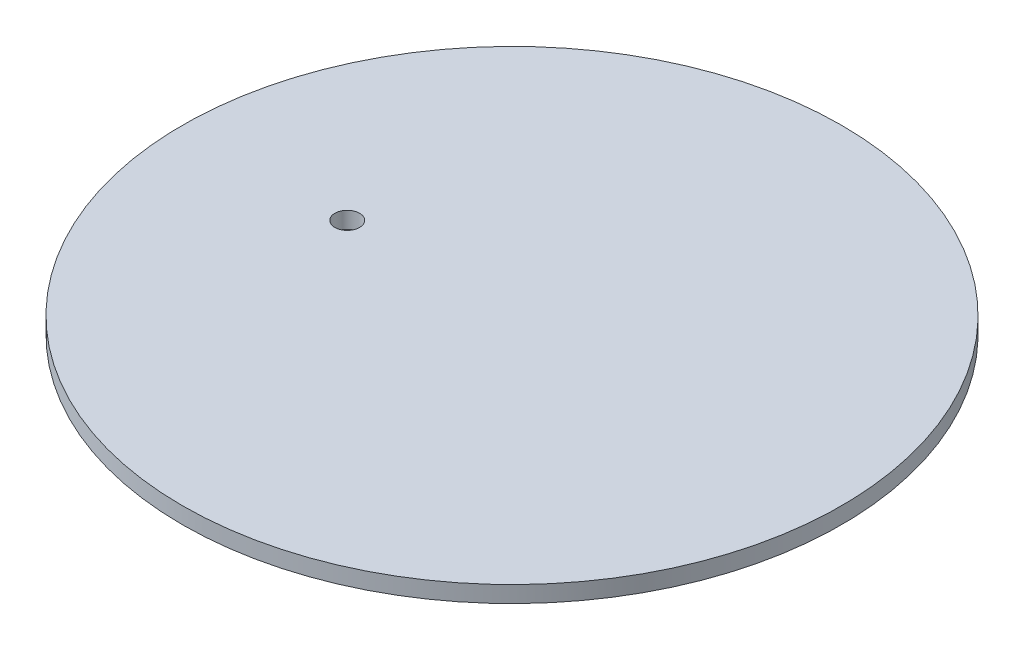
SolidWorks part; units mm, degrees
ref_plane "Front Plane" through (0, 0, 0) normal (0, 0, 1) x (1, 0, 0)
ref_plane "Top Plane" through (0, 0, 0) normal (0, 1, 0) x (1, 0, 0)
ref_plane "Right Plane" through (0, 0, 0) normal (1, 0, 0) x (0, 0, -1)
sketch "Sketch1" plane through (0, 0, 0) normal (0, 1, 0) x (1, 0, 0)
  circle A0 centre (0, 0) radius 127
  dimension "D1" = 254
extrude "Boss-Extrude1" add sketch "Sketch1" along normal blind 6.35
sketch "Sketch2" plane through (0, 6.35, 0) normal (0, 1, 0) x (1, 0, 0)
  circle A0 centre (-63.5, 0) radius 4.7625
  dimension "D1" = 63.5
  dimension "D2" = 9.525
extrude "Cut-Extrude1" cut sketch "Sketch2" against normal through all
